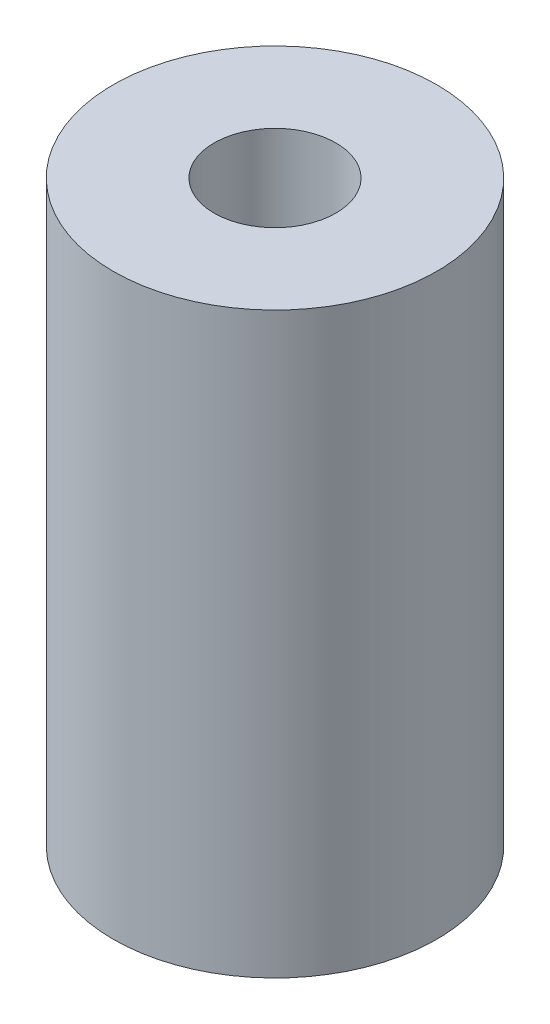
SolidWorks part; units mm, degrees
material "AP"
ref_plane "Front Plane" through (0, 0, 0) normal (0, 0, 1) x (1, 0, 0)
ref_plane "Top Plane" through (0, 0, 0) normal (0, 1, 0) x (1, 0, 0)
ref_plane "Right Plane" through (0, 0, 0) normal (1, 0, 0) x (0, 0, -1)
sketch "Sketch2" plane through (0, 0, 0) normal (0, 1, 0) x (1, 0, 0)
  circle A0 centre (0, 0) radius 42.6085
  circle A1 centre (0, 0) radius 16.0401
  dimension "D1" = 85.217
  dimension "D2" = 32.0802
extrude "Extrude1" add sketch "Sketch2" along normal blind 152.4
